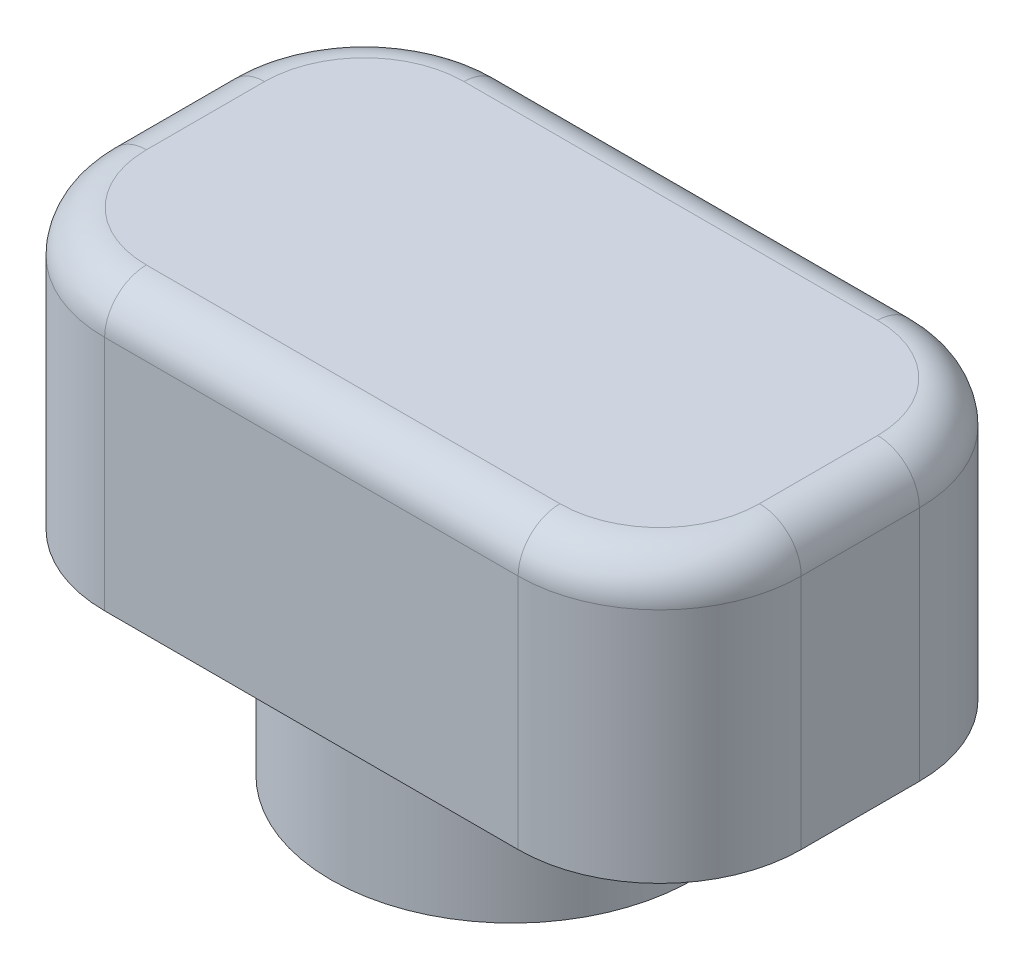
SolidWorks part; units mm, degrees
ref_plane "Front Plane" through (0, 0, 0) normal (0, 0, 1) x (1, 0, 0)
ref_plane "Top Plane" through (0, 0, 0) normal (0, 1, 0) x (1, 0, 0)
ref_plane "Right Plane" through (0, 0, 0) normal (1, 0, 0) x (0, 0, -1)
sketch "Sketch1" plane through (0, 0, 0) normal (0, 1, 0) x (1, 0, 0)
  circle A0 centre (0, 0) radius 3.25
  dimension "D1" = 6.5
extrude "Boss-Extrude1" add sketch "Sketch1" along normal blind 2.5 contours A0
sketch "Sketch2" plane through (0, 0, 0) normal (0, -1, 0) x (1, 0, 0)
  circle A1 centre (0, 0) radius 1.75
  dimension "D1" = 3.5
extrude "Cut-Extrude1" cut sketch "Sketch2" against normal blind 2.5
sketch "Sketch3" plane through (0, 2.5, 0) normal (0, 1, 0) x (1, 0, 0)
  line L1 (-6.25, 3.6) -> (6.25, 3.6)
  line L2 (-6.25, 3.6) -> (-6.25, -3.6)
  line L3 (-6.25, -3.6) -> (6.25, -3.6)
  line L4 (6.25, 3.6) -> (6.25, -3.6)
  line L5 (-6.25, 3.6) -> (6.25, -3.6) construction
  line L6 (-6.25, -3.6) -> (6.25, 3.6) construction
  point P0 (0, 0)
  dimension "D1" = 12.5
  dimension "D2" = 7.2
extrude "Boss-Extrude2" add sketch "Sketch3" along normal blind 5
fillet "Fillet1" radius 2.54 4 edges at (-6.25, 5, -3.6) (6.25, 5, -3.6) (6.25, 5, 3.6) (-6.25, 5, 3.6)
fillet "Fillet2" radius 0.75 8 edges at (6.25, 7.5, 0) (5.5061, 7.5, 2.8561) (5.5061, 7.5, -2.8561) (0, 7.5, -3.6) (-5.5061, 7.5, -2.8561) (-6.25, 7.5, 0) (-5.5061, 7.5, 2.8561) (0, 7.5, 3.6)
